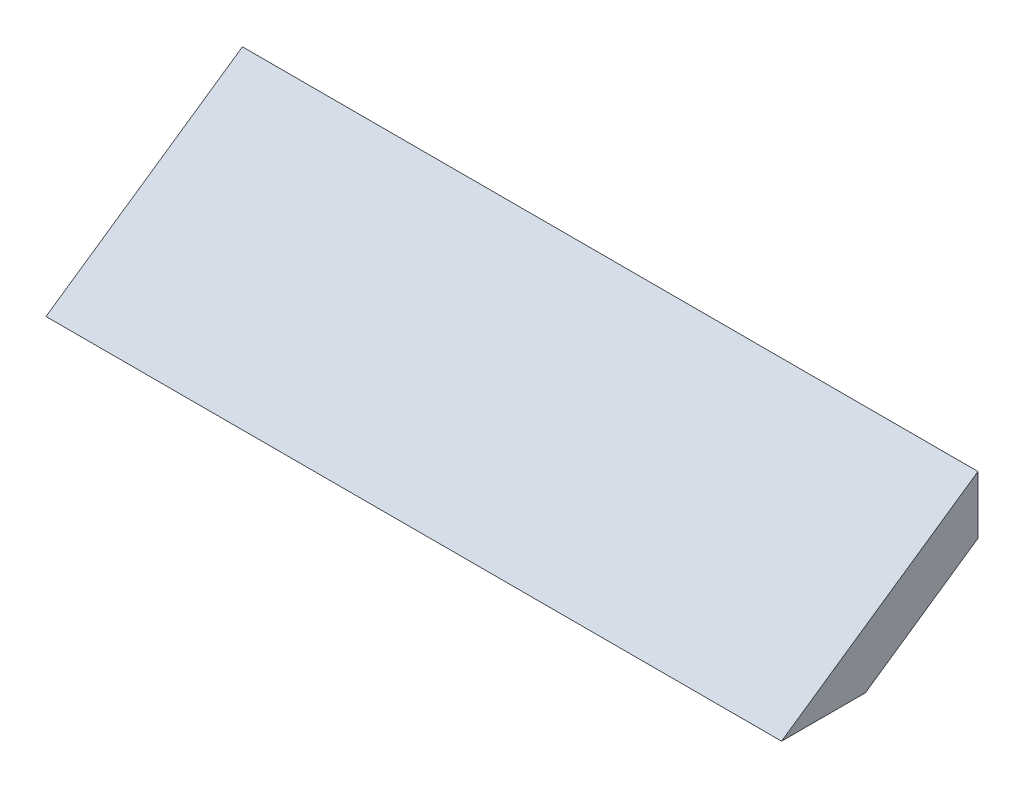
SolidWorks part; units mm, degrees
ref_plane "Front Plane" through (0, 0, 0) normal (0, 0, 1) x (1, 0, 0)
ref_plane "Top Plane" through (0, 0, 0) normal (0, 1, 0) x (1, 0, 0)
ref_plane "Right Plane" through (0, 0, 0) normal (1, 0, 0) x (0, 0, -1)
sketch "Sketch1" plane through (0, 0, 0) normal (0, 0, 1) x (1, 0, 0)
  line L1 (-700, -55) -> (700, -55)
  line L2 (-700, -55) -> (-700, 55)
  line L3 (-700, 55) -> (700, 55)
  line L4 (700, -55) -> (700, 55)
  line L5 (-700, -55) -> (700, 55) construction
  line L6 (-700, 55) -> (700, -55) construction
  point P0 (0, 0)
  dimension "D1" = 1400
  dimension "D2" = 110
sketch "Sketch2" plane through (0, 0, 0) normal (1, 0, 0) x (0, 0, -1)
  line L4 (0, -52.724) -> (-373.8266, -310.3594)
  point P0 (-373.8266, -310.3594)
sweep "Sweep2" add profiles "Sketch1" path "Sketch2"
sketch "Sketch3" plane through (0, 0, 0) normal (1, 0, 0) x (0, 0, -1)
  line L1 (-373.8266, -202.6354) -> (-132.5974, -202.6354)
  line L2 (-373.8266, -202.6354) -> (-373.8266, -321.1086)
  line L3 (-373.8266, -321.1086) -> (-132.5974, -321.1086)
  line L4 (-132.5974, -202.6354) -> (-132.5974, -321.1086)
extrude "Cut-Extrude1" cut sketch "Sketch3" along normal blind 3000
sketch "Sketch4" plane through (0, 0, 0) normal (1, 0, 0) x (0, 0, -1)
  line L1 (-373.8266, -202.6354) -> (-110.7461, -202.6354)
  line L2 (-373.8266, -202.6354) -> (-373.8266, -332.9707)
  line L3 (-373.8266, -332.9707) -> (-110.7461, -332.9707)
  line L4 (-110.7461, -202.6354) -> (-110.7461, -332.9707)
extrude "Cut-Extrude2" cut sketch "Sketch4" against normal blind 1000
